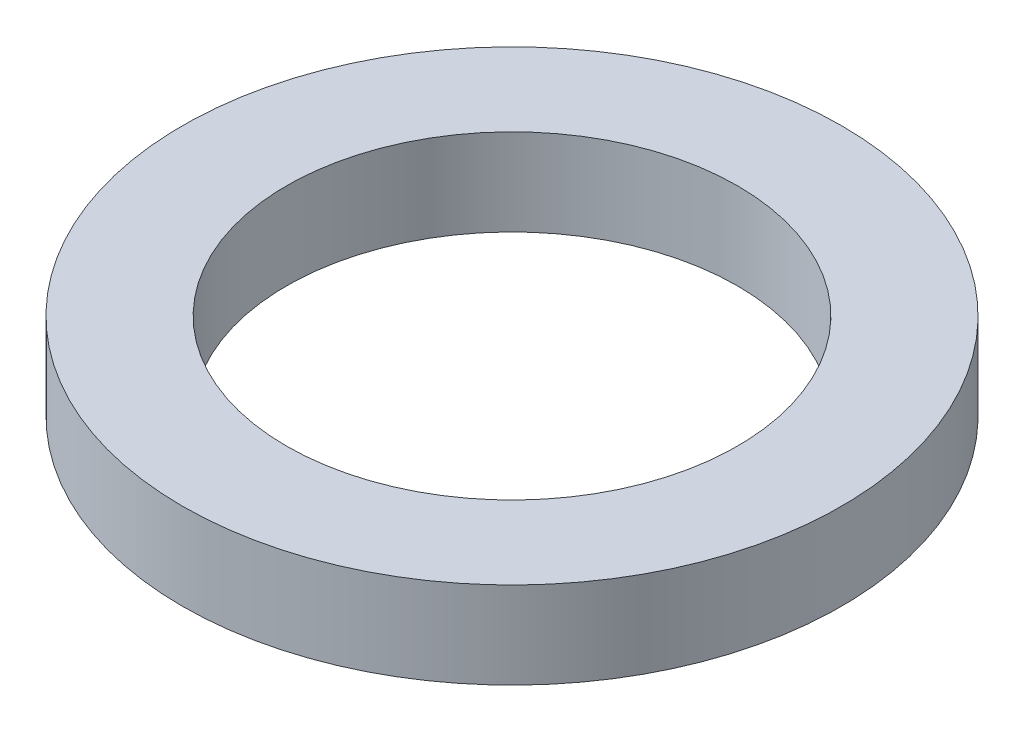
SolidWorks part; units mm, degrees
ref_plane "Спереди" through (0, 0, 0) normal (0, 0, 1) x (1, 0, 0)
ref_plane "Сверху" through (0, 0, 0) normal (0, 1, 0) x (1, 0, 0)
ref_plane "Справа" through (0, 0, 0) normal (1, 0, 0) x (0, 0, -1)
sketch "Эскиз1" plane through (0, 0, 0) normal (0, 1, 0) x (1, 0, 0)
  circle A0 centre (0, 0) radius 2.6
  circle A1 centre (0, 0) radius 3.8
extrude "Бобышка-Вытянуть1" add sketch "Эскиз1" along normal blind 1
